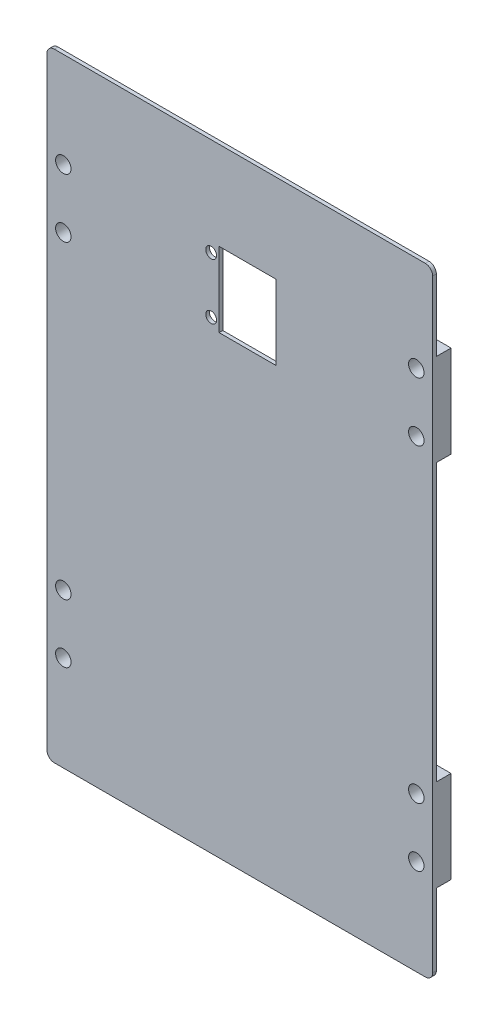
SolidWorks part; units mm, degrees
ref_plane "Front Plane" through (0, 0, 0) normal (0, 0, 1) x (1, 0, 0)
ref_plane "Top Plane" through (0, 0, 0) normal (0, 1, 0) x (1, 0, 0)
ref_plane "Right Plane" through (0, 0, 0) normal (1, 0, 0) x (0, 0, -1)
sketch "Sketch1" plane through (0, 0, 0) normal (0, 0, 1) x (1, 0, 0)
  line L1 (0, -100.2) -> (104.9, -100.2)
  line L2 (0, -100.2) -> (0, 67.9)
  line L3 (0, 67.9) -> (104.9, 67.9)
  line L4 (104.9, -100.2) -> (104.9, 67.9)
extrude "Boss-Extrude1" add sketch "Sketch1" along normal blind 1 from offset 4
sketch "Sketch2" plane through (0, 0, 4) normal (0, 0, -1) x (-1, 0, 0)
  line L0 (-100.45, -58.25) -> (-100.45, -74.25) construction
  line L1 (-4.45, -58.25) -> (-4.45, -74.25) construction
  line L2 (-100.45, 41.95) -> (-100.45, 25.95) construction
  line L3 (-4.45, 41.95) -> (-4.45, 25.95) construction
  line L4 (-104.9, -100.2) -> (-104.9, 67.9) construction
  line L5 (-104.9, 46.45) -> (-96, 46.45)
  line L6 (-104.9, 46.45) -> (-104.9, 21.45)
  line L7 (-104.9, 21.45) -> (-96, 21.45)
  line L8 (-96, 46.45) -> (-96, 21.45)
  line L9 (0, 67.9) -> (0, -100.2) construction
  line L10 (0, 46.45) -> (-8.9, 46.45)
  line L11 (0, 46.45) -> (0, 21.45)
  line L12 (0, 21.45) -> (-8.9, 21.45)
  line L13 (-8.9, 46.45) -> (-8.9, 21.45)
  line L15 (0, -53.75) -> (-8.9, -53.75)
  line L16 (0, -53.75) -> (0, -78.75)
  line L17 (0, -78.75) -> (-8.9, -78.75)
  line L18 (-8.9, -53.75) -> (-8.9, -78.75)
  line L19 (-104.9, -53.75) -> (-96, -53.75)
  line L20 (-104.9, -53.75) -> (-104.9, -78.75)
  line L21 (-104.9, -78.75) -> (-96, -78.75)
  line L22 (-96, -53.75) -> (-96, -78.75)
  circle A1 centre (-100.45, -74.25) radius 1.95 construction
  circle A2 centre (-100.45, -58.25) radius 1.95 construction
  circle A3 centre (-4.45, -74.25) radius 1.95 construction
  circle A4 centre (-4.45, -58.25) radius 1.95 construction
  circle A5 centre (-4.45, 25.95) radius 1.95 construction
  circle A6 centre (-4.45, 41.95) radius 1.95 construction
  circle A7 centre (-100.45, 25.95) radius 1.95 construction
  circle A8 centre (-100.45, 41.95) radius 1.95 construction
  circle A9 centre (-100.45, -74.25) radius 1.95 construction
  circle A10 centre (-100.45, -58.25) radius 1.95 construction
  circle A11 centre (-4.45, -74.25) radius 1.95 construction
  circle A12 centre (-4.45, -58.25) radius 1.95 construction
  circle A13 centre (-4.45, 25.95) radius 1.95 construction
  circle A14 centre (-4.45, 41.95) radius 1.95 construction
  circle A15 centre (-100.45, 25.95) radius 1.95 construction
  circle A16 centre (-100.45, 41.95) radius 1.95 construction
  point P36 (-4.45, 33.95)
  point P37 (-8.9, 33.95)
  point P38 (-100.45, 33.95)
  point P39 (-96, 33.95)
  point P40 (-4.45, -66.25)
  point P41 (-8.9, -66.25)
  point P42 (-100.45, -66.25)
  point P43 (-96, -66.25)
  point P44 (-100.45, -78.75)
  dimension "D1" = 25
extrude "Boss-Extrude2" add sketch "Sketch2" along normal up to surface (4 mm away)
sketch "Sketch5" plane through (0, 0, 5) normal (0, 0, 1) x (1, 0, 0)
  circle A0 centre (100.45, -74.25) radius 2.1
  circle A1 centre (100.45, -58.25) radius 2.1
  circle A2 centre (4.45, -74.25) radius 2.1
  circle A3 centre (4.45, -58.25) radius 2.1
  circle A4 centre (4.45, 25.95) radius 2.1
  circle A5 centre (4.45, 41.95) radius 2.1
  circle A6 centre (100.45, 25.95) radius 2.1
  circle A7 centre (100.45, 41.95) radius 2.1
  dimension "D1" = 4.2
extrude "Cut-Extrude5" cut sketch "Sketch5" against normal through all
sketch "Sketch3" plane through (0, 0, 5) normal (0, 0, 1) x (1, 0, 0)
  line L0 (104.9, 67.9) -> (0, 67.9) construction
  line L1 (62.356, 43.856) -> (42.036, 43.856) construction
  line L2 (62.356, 43.856) -> (62.356, 23.536) construction
  line L3 (62.356, 23.536) -> (42.036, 23.536) construction
  line L4 (42.036, 43.856) -> (42.036, 23.536) construction
  line L5 (100.45, 25.95) -> (100.45, 41.95) construction
  line L6 (44.661, 41.316) -> (44.661, 26.076) construction
  line L7 (62.356, 23.536) -> (46.836, 23.536)
  line L8 (62.356, 23.536) -> (62.356, 43.856)
  line L9 (62.356, 43.856) -> (46.836, 43.856)
  line L10 (46.836, 23.536) -> (46.836, 43.856)
  circle A1 centre (44.661, 26.076) radius 1.475
  circle A2 centre (44.661, 41.316) radius 1.475
  point P4 (52.45, 33.95)
  point P5 (100.45, 33.95)
  point P10 (52.45, 67.9)
  point P15 (42.036, 33.696)
  point P16 (44.661, 33.696)
  dimension "D6" = 2.95
  dimension "D1" = 10.414
  dimension "D2" = 20.32
  dimension "D3" = 20.32
  dimension "D4" = 9.906
  dimension "D5" = 4.8
  dimension "D7" = 2.625
  dimension "D8" = 15.24
extrude "Cut-Extrude3" cut sketch "Sketch3" against normal up to next
fillet "Fillet1" radius 2 4 edges at (0, 67.9, 4.5) (0, -100.2, 4.5) (104.9, -100.2, 4.5) (104.9, 67.9, 4.5)
equation "\"width\"= 24"
equation "\"thk\"= 3"
equation "\"holesize\"= 4.2"
equation "\"holedistance\"= ( 20 + 12 ) / 2"
equation "\"threaded_hole\"= 3.9"
equation "\"fillet_radius\"= 2"
equation "\"ground_clearance\"= 25"
equation "\"tire_thk\"= 3"
equation "\"innerwheel_diam\" = \"wheel_diam\"-2*\"tire_thk\""
equation "\"innerwheel_thk\"= 8"
equation "\"wheel_diam\"= 2*(\"width\"/2+\"ground_clearance\")"
equation "\"D1@Sketch5\"=\"holesize\""
equation "\"coloursensor_holesize\"= 2.65"
equation "\"D6@Sketch3\"=\"coloursensor_holesize\"+0.3"
equation "\"D1@Fillet1\"=\"fillet_radius\""
equation "\"hole_to_edge\" = 4"
